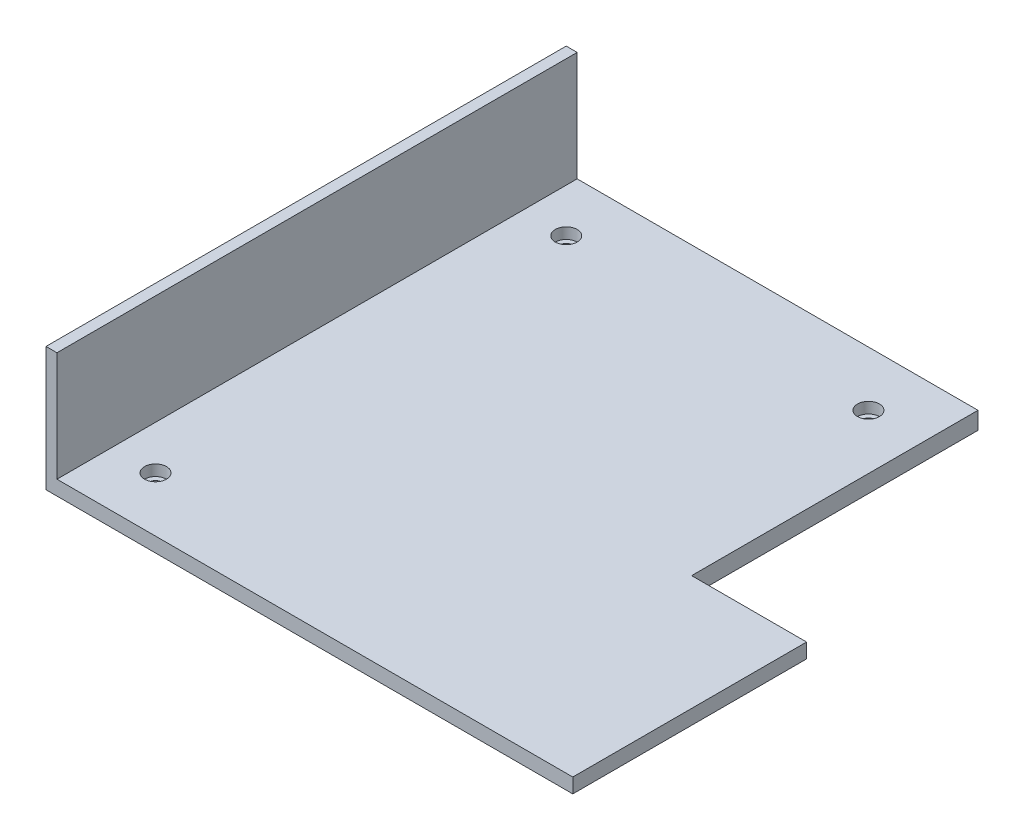
SolidWorks part; units mm, degrees
ref_plane "Front Plane" through (0, 0, 0) normal (0, 0, 1) x (1, 0, 0)
ref_plane "Top Plane" through (0, 0, 0) normal (0, 1, 0) x (1, 0, 0)
ref_plane "Right Plane" through (0, 0, 0) normal (1, 0, 0) x (0, 0, -1)
sketch "Sketch1" plane through (0, 0, 0) normal (0, 1, 0) x (1, 0, 0)
  line L1 (-96.2, 95) -> (96.2, 95)
  line L2 (-96.2, 95) -> (-96.2, -95)
  line L3 (-96.2, -95) -> (96.2, -95)
  line L4 (96.2, 95) -> (96.2, -95)
  line L5 (-96.2, 95) -> (96.2, -95) construction
  line L6 (-96.2, -95) -> (96.2, 95) construction
  point P0 (0, 0)
  dimension "D1" = 190
  dimension "D2" = 192.4
extrude "Boss-Extrude1" add sketch "Sketch1" along normal blind 6.35
sketch "Sketch2" plane through (0, 6.35, 0) normal (0, 1, 0) x (1, 0, 0)
  line L2 (-92.2, 91) -> (-92.2, -91)
  line L4 (96.2, -95) -> (96.2, 95)
  line L5 (96.2, 95) -> (-96.2, 95)
  line L6 (-96.2, 95) -> (-96.2, -95)
  line L7 (-96.2, -95) -> (96.2, -95)
  line L10 (-96.2, 95) -> (-96.2, -95)
  line L12 (92.2, 91) -> (-92.2, 91) construction
  line L13 (96.2, 95) -> (-96.2, 95) construction
  line L14 (92.2, -91) -> (92.2, 91) construction
  line L15 (96.2, -95) -> (96.2, 95) construction
  line L16 (-92.2, 91) -> (-92.2, 95)
  line L17 (96.2, 95) -> (-96.2, 95) construction
  line L18 (-92.2, 95) -> (-96.2, 95)
  line L22 (-92.2, -91) -> (92.2, -91) construction
  line L23 (-96.2, -95) -> (96.2, -95) construction
  line L24 (-92.2, -91) -> (-92.2, -95)
  line L25 (-96.2, -95) -> (96.2, -95) construction
  line L26 (-92.2, -95) -> (-96.2, -95)
  dimension "D1" = 0
  dimension "D2" = 4
extrude "Boss-Extrude2" add sketch "Sketch2" along normal blind 40
sketch "Sketch4" plane through (0, 6.35, 0) normal (0, 1, 0) x (1, 0, 0)
  line L0 (-92.2, -95) -> (96.2, -95) construction
  line L1 (96.2, 95) -> (54.2, 95)
  line L2 (96.2, 95) -> (96.2, -9.6)
  line L3 (96.2, -9.6) -> (54.2, -9.6)
  line L4 (54.2, 95) -> (54.2, -9.6)
  line L5 (-96.2, 95) -> (-96.2, -95) construction
  dimension "D1" = 85.4
  dimension "D2" = 150.4
extrude "Cut-Extrude1" cut sketch "Sketch4" against normal up to next
sketch "Sketch5" plane through (0, 6.35, 0) normal (0, 1, 0) x (1, 0, 0)
  line L0 (-96.2, 95) -> (-96.2, -95) construction
  line L1 (54.2, 95) -> (-96.2, 95) construction
  line L2 (54.2, 95) -> (54.2, 55) construction
  line L3 (54.2, 55) -> (-96.2, 55) construction
  line L4 (-96.2, 95) -> (-96.2, 55) construction
  line L5 (-92.2, -95) -> (96.2, -95) construction
  line L6 (-96.2, 95) -> (-56.2, 95) construction
  line L7 (-96.2, 95) -> (-96.2, -95) construction
  line L8 (-96.2, -95) -> (-56.2, -95) construction
  line L9 (-56.2, 95) -> (-56.2, -95) construction
  line L10 (-76.2, -95) -> (-76.2, 95) construction
  line L11 (54.2, 75) -> (-96.2, 75) construction
  point P18 (-76.2, 75)
  point P20 (-76.2, -75)
  point P24 (34.2, 75)
  dimension "D1" = 40
  dimension "D2" = 40
  dimension "D3" = 20
  dimension "D4" = 20
hole_wizard "CBORE for M4 SHCS1" positions "Sketch5" profile "Sketch6" counterbore size "M4" standard "ANSI Metric" end condition up to next
sketch "Sketch6" plane through (34.2, 6.35, -75) normal (1, 0, 0) x (0, 0, 1)
  line L0 (0, 0) -> (0, 6.35)
  line L1 (0, 6.35) -> (2.25, 6.35)
  line L3 (2.25, 6.35) -> (2.25, 4)
  line L4 (2.25, 4) -> (4, 4)
  line L5 (4, 4) -> (4, 0)
  line L7 (4, 0) -> (0, 0)
  line L11 (0, -6.35) -> (0, 107.95) construction
  dimension "Thru Hole Dia." = 4.5
  dimension "Thru Hole Depth" = 6.35
  dimension "C'Bore Dia." = 8
  dimension "C'Bore Depth" = 4
chamfer "Chamfer1" distance 1 angle 45 2 edges at (96.2, 0, 52.3) (0, 0, 95)
mirror "Mirror1" [suppressed]
delete or keep bodies "Body-Delete/Keep 1" [suppressed] type delete bodies bodies 105
equation "\"D2@Sketch1\"=384.8/2"
equation "\"D2@Sketch4\"=152.4-2"
equation "\"D1@Sketch4\"=87.4-2"
